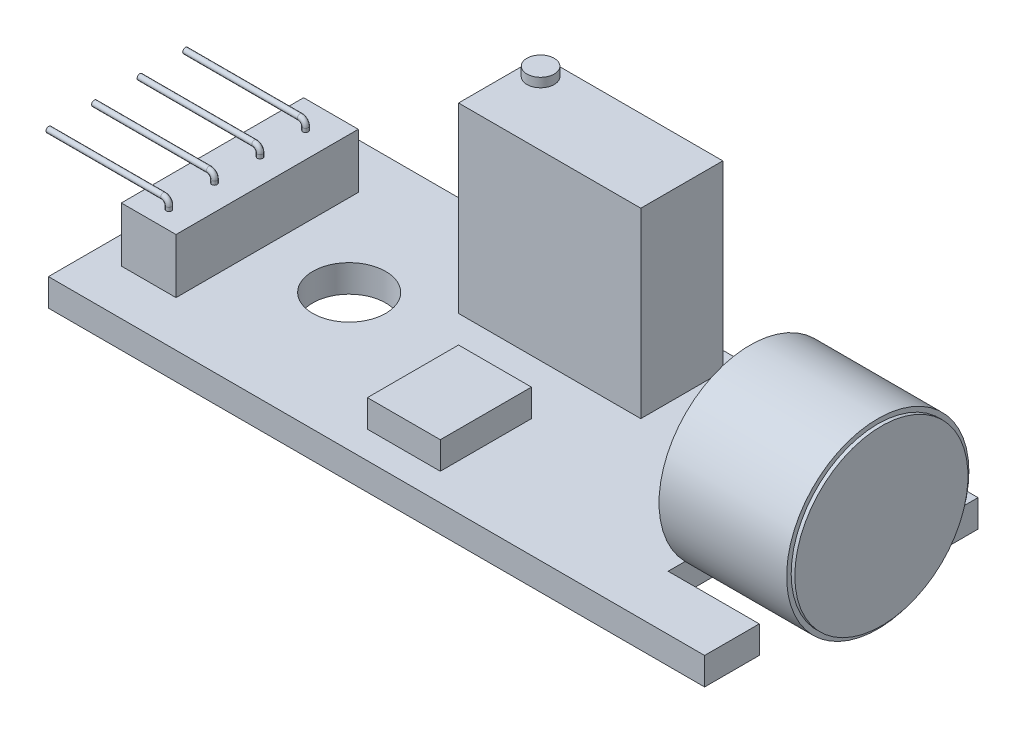
SolidWorks part; units mm, degrees
ref_plane "Front Plane" through (0, 0, 0) normal (0, 0, 1) x (1, 0, 0)
ref_plane "Top Plane" through (0, 0, 0) normal (0, 1, 0) x (1, 0, 0)
ref_plane "Right Plane" through (0, 0, 0) normal (1, 0, 0) x (0, 0, -1)
sketch "Sketch1" plane through (0, 0, 0) normal (0, 1, 0) x (1, 0, 0)
  line L0 (18, 4.5) -> (13, 4.5)
  line L1 (-18, -7.5) -> (18, -7.5)
  line L2 (-18, -7.5) -> (-18, 7.5)
  line L3 (-18, 7.5) -> (18, 7.5)
  line L4 (18, -7.5) -> (18, -4.5)
  line L5 (-18, -7.5) -> (18, 7.5) construction
  line L6 (-18, 7.5) -> (18, -7.5) construction
  line L7 (13, 4.5) -> (13, -4.5)
  line L8 (13, -4.5) -> (18, -4.5)
  line L9 (-22.4835, 0) -> (23.2259, 0) construction
  line L10 (18, 4.5) -> (18, 7.5)
  circle A0 centre (-9, 0) radius 2
  point P0 (0, 0)
  dimension "D5" = 9
  dimension "D6" = 4
  dimension "D1" = 36
  dimension "D2" = 15
  dimension "D3" = 9
  dimension "D4" = 5
extrude "Boss-Extrude1" add sketch "Sketch1" along normal blind 1.5
sketch "Sketch2" plane through (13, 0, 0) normal (1, 0, 0) x (0, 0, -1)
  line L0 (0, 13.2627) -> (0, -7.0663) construction
  line L1 (-10.2537, 0) -> (8.6802, 0) construction
  circle A0 centre (0, 5) radius 5
  circle A1 centre (0, 5) radius 4.75
  dimension "D1" = 10
  dimension "D2" = 9.5
extrude "Boss-Extrude2" add sketch "Sketch2" along normal blind 7
sketch "Sketch3" plane through (13, 0, 0) normal (-1, 0, 0) x (0, 0, 1)
  circle A0 centre (0, 5) radius 4.75 construction
  circle A1 centre (0, 5) radius 4.75
extrude "Boss-Extrude3" add sketch "Sketch3" against normal blind 7.2
sketch "Sketch4" plane through (0, 1.5, 0) normal (0, 1, 0) x (1, 0, 0)
  line L0 (-18, 7.5) -> (-18, -7.5) construction
  line L1 (5, 2) -> (-5, 2)
  line L2 (5, 2) -> (5, 6.5)
  line L3 (5, 6.5) -> (-5, 6.5)
  line L4 (-5, 2) -> (-5, 6.5)
  line L5 (5, 2) -> (-5, 6.5) construction
  line L6 (5, 6.5) -> (-5, 2) construction
  line L7 (18, 7.5) -> (-18, 7.5) construction
  point P0 (0, 4.25)
  dimension "D1" = 13
  dimension "D2" = 10
  dimension "D3" = 4.5
  dimension "D4" = 1
extrude "Boss-Extrude4" add sketch "Sketch4" along normal blind 10
sketch "Sketch5" plane through (0, 1.5, 0) normal (0, 1, 0) x (1, 0, 0)
  line L0 (25.9181, 0) -> (-22.4844, 0) construction
  line L1 (-18, 7.5) -> (-18, -7.5) construction
  line L2 (-13.5, -5) -> (-16.5, -5)
  line L3 (-13.5, -5) -> (-13.5, 5)
  line L4 (-13.5, 5) -> (-16.5, 5)
  line L5 (-16.5, -5) -> (-16.5, 5)
  line L6 (-13.5, -5) -> (-16.5, 5) construction
  line L7 (-13.5, 5) -> (-16.5, -5) construction
  point P3 (-15, 0)
  dimension "D1" = 10
  dimension "D2" = 3
  dimension "D3" = 1.5
extrude "Boss-Extrude5" add sketch "Sketch5" along normal blind 3
sketch "Sketch6" plane through (0, 1.5, 0) normal (0, 1, 0) x (1, 0, 0)
  line L0 (0, -9.808) -> (0, 13.0568) construction
  line L1 (-18, -7.5) -> (18, -7.5) construction
  line L2 (2, -1) -> (-2, -1)
  line L3 (2, -1) -> (2, -6)
  line L4 (2, -6) -> (-2, -6)
  line L5 (-2, -1) -> (-2, -6)
  line L6 (2, -1) -> (-2, -6) construction
  line L7 (2, -6) -> (-2, -1) construction
  point P3 (0, -3.5)
  dimension "D1" = 4
  dimension "D2" = 5
  dimension "D3" = 1.5
extrude "Boss-Extrude6" add sketch "Sketch6" along normal blind 1.5
sketch3d "3DSketch1"
  line L0 (13, 5.7407, -1) -> (12.5, 5.7407, -1)
  line L1 (11.5, 4.7407, -1) -> (11.5, 1.5, -1)
  arc A2 (12.5, 5.7407, -1) -> (11.5, 4.7407, -1) centre (12.5, 4.7407, -1) ccw
  point P8 (11.5, 5.7407, -1)
  point P10 (12.5, 4.7407, 0)
  dimension "D3" = 1
  dimension "D1" = 1
  dimension "D2" = 1.5
sweep "Sweep1" add path "3DSketch1" circular profile diameter 0.3 parameters "D3"=0.3
sketch3d "3DSketch2"
  line L0 (-14.8919, 4.5, 4) -> (-14.8919, 4.7, 4)
  line L1 (-15.1919, 5, 4) -> (-21.4832, 5, 4)
  arc A0 (-14.8919, 4.7, 4) -> (-15.1919, 5, 4) centre (-15.1919, 4.7, 4) ccw
  point P8 (-14.8919, 5, 4)
  point P9 (-15.1919, 4.7, 4.3)
  dimension "D3" = 0.3
  dimension "D1" = 4
  dimension "D2" = 0.5
sweep "Sweep2" add path "3DSketch2" circular profile diameter 0.3 parameters "D3"=0.3
pattern_linear "LPattern1" count 4 spacing 2.5 along (0, 0, -1) of "Sweep2"
mirror "Mirror1" about plane through (0, 0, 0) normal (0, 0, 1) of "Sweep1"
sketch "Sketch63" plane through (0, 11.5, 0) normal (0, 1, 0) x (1, 0, 0)
  line L0 (5, 6.5) -> (-5, 6.5) construction
  line L1 (-5, 6.5) -> (-5, 2) construction
  circle A0 centre (-4, 5.5) radius 0.75
  dimension "D1" = 1.5
  dimension "D2" = 1
  dimension "D3" = 1
extrude "Boss-Extrude7" add sketch "Sketch63" along normal blind 0.5
